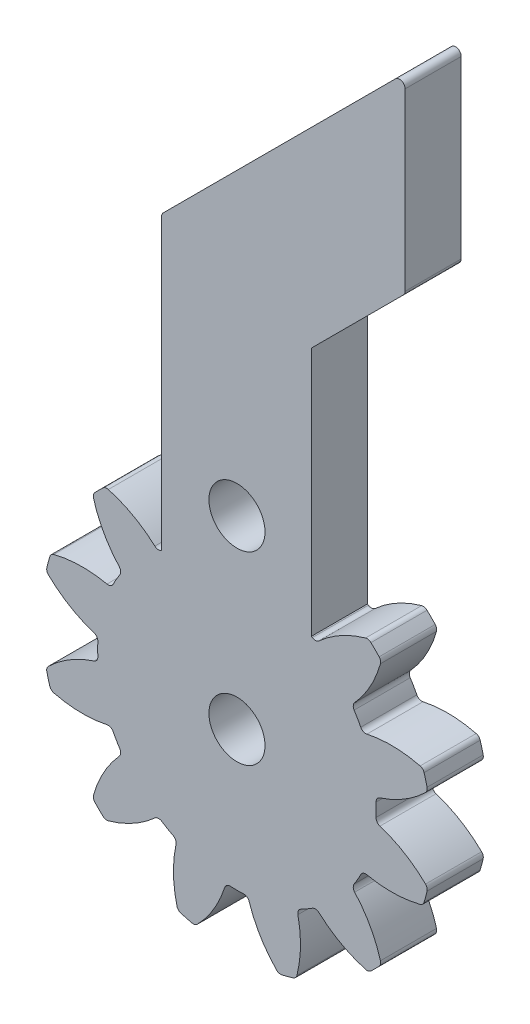
SolidWorks part; units mm, degrees
ref_plane "Plan de face" through (0, 0, 0) normal (0, 0, 1) x (1, 0, 0)
ref_plane "Plan de dessus" through (0, 0, 0) normal (0, 1, 0) x (1, 0, 0)
ref_plane "Plan de droite" through (0, 0, 0) normal (1, 0, 0) x (0, 0, -1)
sketch "Esquisse18" plane through (0, 0, 0) normal (0, 0, 1) x (1, 0, 0)
  line L0 (88.0303, -5.3051) -> (86.9697, -4.2444) construction
  line L1 (88.0303, -5.3051) -> (86.7313, -4.5551) construction
  line L2 (88.0303, -5.3051) -> (87.2803, -4.0061) construction
  line L3 (83.9962, 16.5609) -> (97.0256, 29.5903)
  line L4 (86.7313, -4.5551) -> (77.8105, 0.5953) construction
  line L5 (83.9962, 16.5609) -> (83.9962, 0.9583)
  line L7 (92.008, 14.3472) -> (92.008, 0.9941)
  line L8 (97.0256, 29.5903) -> (97.0256, 19.3648)
  line L9 (97.0256, 19.3648) -> (92.008, 14.3472)
  circle A0 centre (88.0303, -5.3051) radius 1.5
  circle A1 centre (88.0303, 4.5908) radius 1.5
  arc A4 (80.3552, 1.5746) -> (81.733, -0.9141) centre (86.3686, 3.278) ccw
  arc A5 (81.1506, 2.37) -> (83.6393, 0.9922) centre (79.4472, -3.6434) cw
  arc A6 (81.7629, -1.2775) -> (81.5784, -1.5801) centre (88.0303, -5.3051) ccw
  arc A7 (80.863, 2.2997) -> (80.4255, 1.8622) centre (88.0303, -5.3051) ccw
  arc A8 (81.1506, 2.37) -> (80.863, 2.2997) centre (81.0688, 2.0814) ccw
  arc A9 (80.3552, 1.5746) -> (80.4255, 1.8622) centre (80.6438, 1.6564) cw
  arc A10 (81.733, -0.9141) -> (81.7629, -1.2775) centre (81.5105, -1.1153) cw
  arc A11 (83.6393, 0.9922) -> (84.0027, 0.9623) centre (83.8405, 1.2147) ccw
  arc A16 (85.9098, 4.7816) -> (85.6257, 4.8645) centre (85.6947, 4.5725) ccw
  arc A29 (92.0579, 0.9623) -> (92.008, 0.9941) centre (88.0303, -5.3051) ccw
  arc A30 (92.4213, 0.9922) -> (92.0579, 0.9623) centre (92.2201, 1.2147) cw
  arc A31 (94.9101, 2.37) -> (92.4213, 0.9922) centre (96.6134, -3.6434) ccw
  arc A32 (94.9101, 2.37) -> (95.1976, 2.2997) centre (94.9918, 2.0814) cw
  arc A33 (95.6351, 1.8622) -> (95.1976, 2.2997) centre (88.0303, -5.3051) ccw
  arc A34 (95.7054, 1.5746) -> (95.6351, 1.8622) centre (95.4168, 1.6564) ccw
  arc A35 (95.7054, 1.5746) -> (94.3276, -0.9141) centre (89.692, 3.278) cw
  arc A36 (94.3276, -0.9141) -> (94.2978, -1.2775) centre (94.5501, -1.1153) ccw
  arc A37 (94.4822, -1.5801) -> (94.2978, -1.2775) centre (88.0303, -5.3051) ccw
  arc A38 (94.652, -1.8911) -> (94.4822, -1.5801) centre (88.0303, -5.3051) ccw
  arc A39 (94.9817, -2.047) -> (94.652, -1.8911) centre (94.9187, -1.7537) cw
  arc A40 (97.8259, -2.0981) -> (94.9817, -2.047) centre (96.2944, -8.1576) ccw
  arc A41 (97.8259, -2.0981) -> (98.0397, -2.3028) centre (97.7524, -2.389) cw
  arc A42 (98.1999, -2.9005) -> (98.0397, -2.3028) centre (88.0303, -5.3051) ccw
  arc A43 (98.117, -3.1846) -> (98.1999, -2.9005) centre (97.9079, -2.9695) ccw
  arc A44 (98.117, -3.1846) -> (95.6795, -4.651) centre (93.7609, 1.2972) cw
  arc A45 (95.6795, -4.651) -> (95.4719, -4.9508) centre (95.7715, -4.9365) ccw
  arc A46 (95.4803, -5.3051) -> (95.4719, -4.9508) centre (88.0303, -5.3051) ccw
  arc A47 (95.4719, -5.6594) -> (95.4803, -5.3051) centre (88.0303, -5.3051) ccw
  arc A48 (95.6795, -5.9592) -> (95.4719, -5.6594) centre (95.7715, -5.6737) cw
  arc A49 (98.117, -7.4256) -> (95.6795, -5.9592) centre (93.7609, -11.9074) ccw
  arc A50 (98.117, -7.4256) -> (98.1999, -7.7097) centre (97.9079, -7.6407) cw
  arc A51 (98.0397, -8.3074) -> (98.1999, -7.7097) centre (88.0303, -5.3051) ccw
  arc A52 (97.8259, -8.5121) -> (98.0397, -8.3074) centre (97.7524, -8.2212) ccw
  arc A53 (97.8259, -8.5121) -> (94.9817, -8.5632) centre (96.2944, -2.4526) cw
  arc A54 (94.9817, -8.5632) -> (94.652, -8.7191) centre (94.9187, -8.8565) ccw
  arc A55 (94.4822, -9.0301) -> (94.652, -8.7191) centre (88.0303, -5.3051) ccw
  arc A56 (94.2978, -9.3327) -> (94.4822, -9.0301) centre (88.0303, -5.3051) ccw
  arc A57 (94.3276, -9.6961) -> (94.2978, -9.3327) centre (94.5501, -9.4949) cw
  arc A58 (95.7054, -12.1848) -> (94.3276, -9.6961) centre (89.692, -13.8882) ccw
  arc A59 (95.7054, -12.1848) -> (95.6351, -12.4724) centre (95.4168, -12.2666) cw
  arc A60 (95.1976, -12.9099) -> (95.6351, -12.4724) centre (88.0303, -5.3051) ccw
  arc A61 (94.9101, -12.9802) -> (95.1976, -12.9099) centre (94.9918, -12.6916) ccw
  arc A62 (94.9101, -12.9802) -> (92.4213, -11.6024) centre (96.6134, -6.9668) cw
  arc A63 (92.4213, -11.6024) -> (92.0579, -11.5725) centre (92.2201, -11.8249) ccw
  arc A64 (91.7553, -11.757) -> (92.0579, -11.5725) centre (88.0303, -5.3051) ccw
  arc A65 (91.4443, -11.9268) -> (91.7553, -11.757) centre (88.0303, -5.3051) ccw
  arc A66 (91.2884, -12.2565) -> (91.4443, -11.9268) centre (91.5817, -12.1935) cw
  arc A67 (91.2373, -15.1007) -> (91.2884, -12.2565) centre (85.1778, -13.5691) ccw
  arc A68 (91.2373, -15.1007) -> (91.0326, -15.3145) centre (90.9464, -15.0272) cw
  arc A69 (90.435, -15.4747) -> (91.0326, -15.3145) centre (88.0303, -5.3051) ccw
  arc A70 (90.1508, -15.3918) -> (90.435, -15.4747) centre (90.3659, -15.1827) ccw
  arc A71 (90.1508, -15.3918) -> (88.6844, -12.9542) centre (94.6326, -11.0357) cw
  arc A72 (88.6844, -12.9542) -> (88.3846, -12.7467) centre (88.3989, -13.0463) ccw
  arc A73 (88.0303, -12.7551) -> (88.3846, -12.7467) centre (88.0303, -5.3051) ccw
  arc A74 (87.676, -12.7467) -> (88.0303, -12.7551) centre (88.0303, -5.3051) ccw
  arc A75 (87.3762, -12.9542) -> (87.676, -12.7467) centre (87.6618, -13.0463) cw
  arc A76 (85.9098, -15.3918) -> (87.3762, -12.9542) centre (81.428, -11.0357) ccw
  arc A77 (85.9098, -15.3918) -> (85.6257, -15.4747) centre (85.6947, -15.1827) cw
  arc A78 (85.028, -15.3145) -> (85.6257, -15.4747) centre (88.0303, -5.3051) ccw
  arc A79 (84.8233, -15.1007) -> (85.028, -15.3145) centre (85.1142, -15.0272) ccw
  arc A80 (84.8233, -15.1007) -> (84.7722, -12.2565) centre (90.8828, -13.5691) cw
  arc A81 (84.7722, -12.2565) -> (84.6164, -11.9268) centre (84.4789, -12.1935) ccw
  arc A82 (84.3053, -11.757) -> (84.6164, -11.9268) centre (88.0303, -5.3051) ccw
  arc A83 (84.0027, -11.5725) -> (84.3053, -11.757) centre (88.0303, -5.3051) ccw
  arc A84 (83.6393, -11.6024) -> (84.0027, -11.5725) centre (83.8405, -11.8249) cw
  arc A85 (81.1506, -12.9802) -> (83.6393, -11.6024) centre (79.4472, -6.9668) ccw
  arc A86 (81.1506, -12.9802) -> (80.863, -12.9099) centre (81.0688, -12.6916) cw
  arc A87 (80.4255, -12.4724) -> (80.863, -12.9099) centre (88.0303, -5.3051) ccw
  arc A88 (80.3552, -12.1848) -> (80.4255, -12.4724) centre (80.6438, -12.2666) ccw
  arc A89 (80.3552, -12.1848) -> (81.733, -9.6961) centre (86.3686, -13.8882) cw
  arc A90 (81.733, -9.6961) -> (81.7629, -9.3327) centre (81.5105, -9.4949) ccw
  arc A91 (81.5784, -9.0301) -> (81.7629, -9.3327) centre (88.0303, -5.3051) ccw
  arc A92 (81.4086, -8.7191) -> (81.5784, -9.0301) centre (88.0303, -5.3051) ccw
  arc A93 (81.0789, -8.5632) -> (81.4086, -8.7191) centre (81.1419, -8.8565) cw
  arc A94 (78.2347, -8.5121) -> (81.0789, -8.5632) centre (79.7663, -2.4526) ccw
  arc A95 (78.2347, -8.5121) -> (78.0209, -8.3074) centre (78.3082, -8.2212) cw
  arc A96 (77.8607, -7.7097) -> (78.0209, -8.3074) centre (88.0303, -5.3051) ccw
  arc A97 (77.9436, -7.4256) -> (77.8607, -7.7097) centre (78.1527, -7.6407) ccw
  arc A98 (77.9436, -7.4256) -> (80.3812, -5.9592) centre (82.2997, -11.9074) cw
  arc A102 (80.3812, -5.9592) -> (80.5887, -5.6594) centre (80.2891, -5.6737) ccw
  arc A104 (80.5803, -5.3051) -> (80.5887, -5.6594) centre (88.0303, -5.3051) ccw
  arc A105 (80.5887, -4.9508) -> (80.5803, -5.3051) centre (88.0303, -5.3051) ccw
  arc A106 (80.3812, -4.651) -> (80.5887, -4.9508) centre (80.2891, -4.9365) cw
  arc A108 (77.9436, -3.1846) -> (80.3812, -4.651) centre (82.2997, 1.2972) ccw
  arc A109 (77.9436, -3.1846) -> (77.8607, -2.9005) centre (78.1527, -2.9695) cw
  arc A110 (78.0209, -2.3028) -> (77.8607, -2.9005) centre (88.0303, -5.3051) ccw
  arc A112 (78.2347, -2.0981) -> (78.0209, -2.3028) centre (78.3082, -2.389) ccw
  arc A114 (78.2347, -2.0981) -> (81.0789, -2.047) centre (79.7663, -8.1576) cw
  arc A115 (81.0789, -2.047) -> (81.4086, -1.8911) centre (81.1419, -1.7537) ccw
  arc A118 (81.5784, -1.5801) -> (81.4086, -1.8911) centre (88.0303, -5.3051) ccw
  arc A131 (85.6257, 4.8645) -> (85.028, 4.7043) centre (88.0303, -5.3051) ccw [skipped]
  arc A132 (84.8233, 4.4905) -> (85.028, 4.7043) centre (85.1142, 4.417) cw [skipped]
  arc A133 (84.8233, 4.4905) -> (84.7722, 1.6463) centre (90.8828, 2.9589) ccw [skipped]
  arc A134 (85.9098, 4.7816) -> (87.3762, 2.344) centre (81.428, 0.4255) cw [skipped]
  arc A136 (88.6844, 2.344) -> (88.3846, 2.1365) centre (88.3989, 2.4361) cw [skipped]
  arc A137 (87.3762, 2.344) -> (87.676, 2.1365) centre (87.6618, 2.4361) ccw [skipped]
  arc A138 (88.3846, 2.1365) -> (88.0303, 2.1449) centre (88.0303, -5.3051) ccw [skipped]
  arc A139 (90.1508, 4.7816) -> (88.6844, 2.344) centre (94.6326, 0.4255) ccw [skipped]
  arc A140 (90.1508, 4.7816) -> (90.435, 4.8645) centre (90.3659, 4.5725) cw [skipped]
  arc A141 (91.0326, 4.7043) -> (90.435, 4.8645) centre (88.0303, -5.3051) ccw [skipped]
  arc A142 (91.2373, 4.4905) -> (91.0326, 4.7043) centre (90.9464, 4.417) ccw [skipped]
  arc A143 (91.2373, 4.4905) -> (91.2884, 1.6463) centre (85.1778, 2.9589) cw [skipped]
  arc A144 (91.2884, 1.6463) -> (91.4443, 1.3166) centre (91.5817, 1.5833) ccw [skipped]
  arc A146 (84.7722, 1.6463) -> (84.6164, 1.3166) centre (84.4789, 1.5833) cw [skipped]
  arc A147 (84.6164, 1.3166) -> (84.3053, 1.1468) centre (88.0303, -5.3051) ccw [skipped]
  point P26 (81.8919, -1.0834)
  point P192 (88.0303, -5.3051)
  point P225 (88.0303, -5.3051)
  dimension "D1" = 3
  dimension "D2" = 12
  dimension "D3" = 15
  dimension "D5" = 3
  dimension "D7" = 12.5
  dimension "D8" = 0.3
  dimension "D6" = 15
extrude "Boss.-Extru.18" add sketch "Esquisse18" along normal blind 3 separate body
fillet "Congé1" radius 0.3 3 edges at (83.9962, 16.5609, 1.5) (97.0256, 19.3648, 1.5) (97.0256, 29.5903, 1.5)
